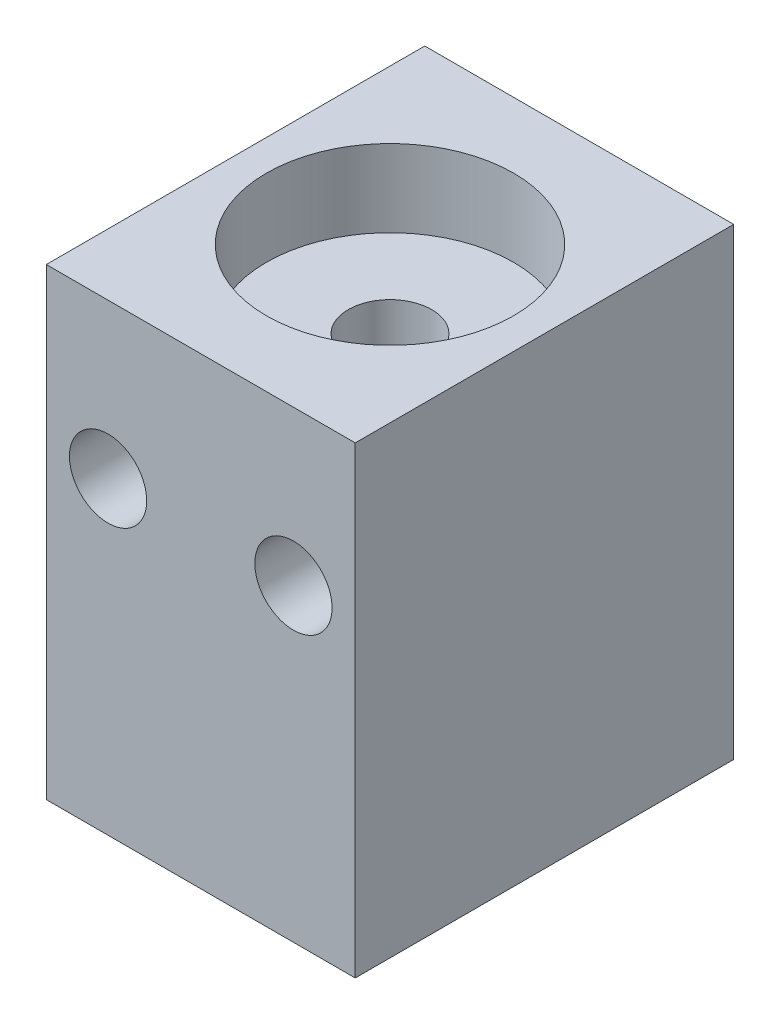
SolidWorks part; units mm, degrees
ref_plane "Front Plane" through (0, 0, 0) normal (0, 0, 1) x (1, 0, 0)
ref_plane "Top Plane" through (0, 0, 0) normal (0, 1, 0) x (1, 0, 0)
ref_plane "Right Plane" through (0, 0, 0) normal (1, 0, 0) x (0, 0, -1)
sketch "Sketch1" plane through (0, 0, 0) normal (0, 0, 1) x (1, 0, 0)
  line L1 (-10, -15) -> (10, -15)
  line L2 (-10, -15) -> (-10, 15)
  line L3 (-10, 15) -> (10, 15)
  line L4 (10, -15) -> (10, 15)
  line L5 (-10, -15) -> (10, 15) construction
  line L6 (-10, 15) -> (10, -15) construction
  point P0 (0, 0)
  dimension "D1" = 20
  dimension "D2" = 30
extrude "Boss-Extrude1" add sketch "Sketch1" along normal mid plane 24.5
sketch "Sketch3" plane through (0, 0, 0) normal (1, 0, 0) x (0, 0, -1)
  line L0 (0, 15) -> (0, -15)
  line L1 (-12.25, 15) -> (12.25, 15) construction
  line L2 (-12.25, -15) -> (12.25, -15) construction
  line L3 (0, 15) -> (8, 15)
  line L4 (8, 15) -> (8, 10)
  line L5 (8, 10) -> (2.7, 10)
  line L6 (2.7, 10) -> (2.7, -10)
  line L7 (2.7, -10) -> (8, -10)
  line L8 (8, -10) -> (8, -15)
  line L9 (8, -15) -> (0, -15)
  dimension "D1" = 5
  dimension "D2" = 8
  dimension "D3" = 2.7
revolve "Cut-Revolve1" cut sketch "Sketch3" angle 360 about L0
sketch "Sketch4" plane through (0, 0, -12.25) normal (0, 0, -1) x (-1, 0, 0)
  line L0 (-6, 5) -> (6, 5) construction
  line L1 (0, 0) -> (0, 5) construction
  line L2 (-10, 15) -> (10, 15) construction
  circle A0 centre (-6, 5) radius 2.5
  circle A1 centre (6, 5) radius 2.5
  dimension "D1" = 5
  dimension "D2" = 10
  dimension "D3" = 12
extrude "Cut-Extrude1" cut sketch "Sketch4" against normal through all
